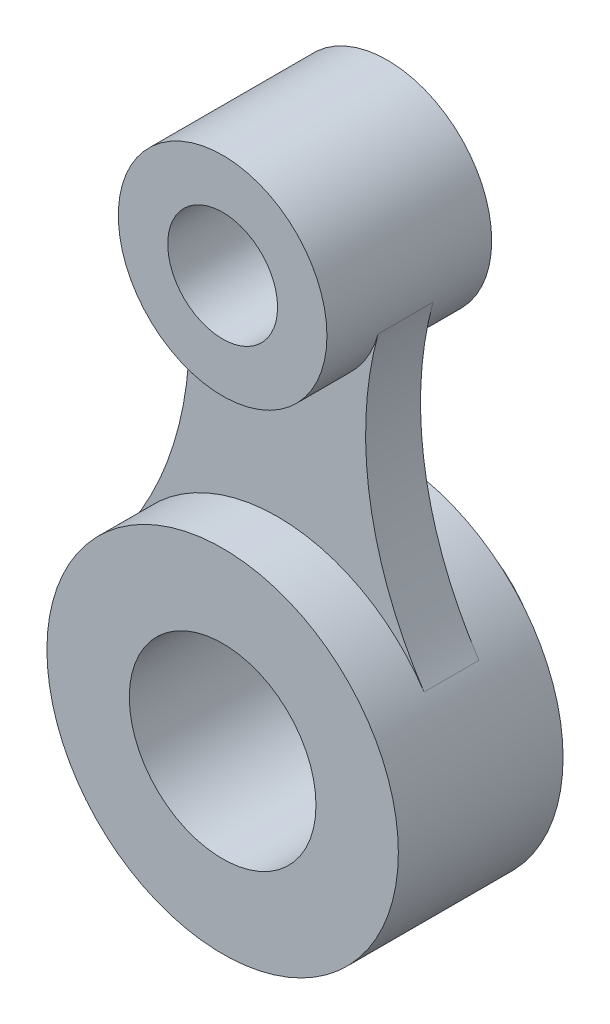
SolidWorks part; units mm, degrees
material "Alliage 1060"
ref_plane "Plan de face" through (0, 0, 0) normal (0, 0, 1) x (1, 0, 0)
ref_plane "Plan de dessus" through (0, 0, 0) normal (0, 1, 0) x (1, 0, 0)
ref_plane "Plan de droite" through (0, 0, 0) normal (1, 0, 0) x (0, 0, -1)
sketch "Esquisse1" plane through (0, 0, 0) normal (0, 0, 1) x (1, 0, 0)
  circle A0 centre (0, 0) radius 32
  circle A1 centre (0, 0) radius 17
  circle A2 centre (0, 75) radius 19
  circle A3 centre (0, 75) radius 10
  dimension "D1" = 64
  dimension "D2" = 34
  dimension "D3" = 20
  dimension "D4" = 38
  dimension "D5" = 75
extrude "Boss.-Extru.1" add sketch "Esquisse1" along normal mid plane 30
sketch "Esquisse2" plane through (0, 0, 0) normal (0, 0, 1) x (1, 0, 0)
  arc A0 (26.6783, 17.6711) -> (-26.6783, 17.6711) centre (0, 0) ccw
  arc A2 (-18.3212, 69.9669) -> (18.3212, 69.9669) centre (0, 75) ccw
  arc A4 (18.3212, 69.9669) -> (26.6783, 17.6711) centre (80.0349, 53.0133) ccw
  arc A5 (-26.6783, 17.6711) -> (-18.3212, 69.9669) centre (-80.0349, 53.0133) ccw
  dimension "D1" = 128
  dimension "D2" = 32
extrude "Boss.-Extru.2" add sketch "Esquisse2" along normal mid plane 10
sketch "Esquisse3" plane through (0, 0, -15) normal (0, 0, -1) x (-1, 0, 0)
  circle A0 centre (0, 0) radius 21.5
  circle A1 centre (0, 0) radius 27.5
  dimension "D1" = 55
  dimension "D2" = 43
extrude "Enlèv. mat.-Extru.1" cut sketch "Esquisse3" against normal blind 5
sketch "Esquisse4" plane through (0, 0, -15) normal (0, 0, -1) x (-1, 0, 0)
  circle A0 centre (0, 0) radius 17 construction
  circle A1 centre (0, 0) radius 21.5
  circle A2 centre (0, 0) radius 21.5
  circle A3 centre (0, 0) radius 17
  dimension "D1" = 0
extrude "Boss.-Extru.3" add sketch "Esquisse4" along normal mid plane 15
